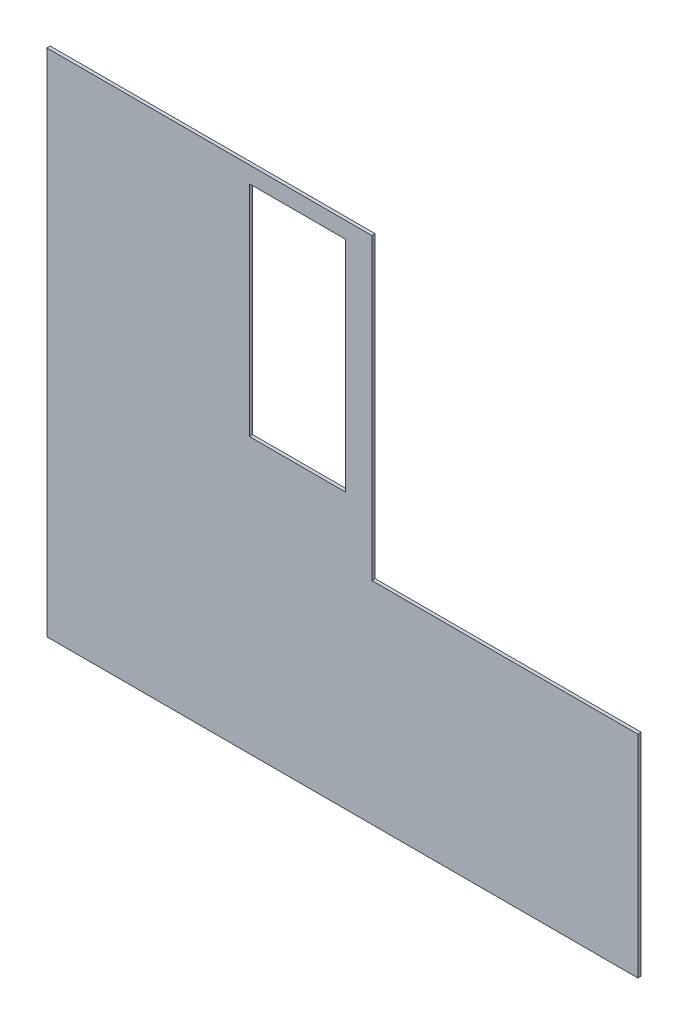
SolidWorks part; units mm, degrees
ref_plane "Plan de face" through (0, 0, 0) normal (0, 0, 1) x (1, 0, 0)
ref_plane "Plan de dessus" through (0, 0, 0) normal (0, 1, 0) x (1, 0, 0)
ref_plane "Plan de droite" through (0, 0, 0) normal (1, 0, 0) x (0, 0, -1)
sketch "Esquisse1" plane through (0, 0, 0) normal (0, 0, 1) x (1, 0, 0)
  line L0 (589.2231, -367.6438) -> (49.2231, -367.6438)
  line L1 (49.2231, 98.3562) -> (346.2231, 98.3562)
  line L2 (49.2231, 98.3562) -> (49.2231, -367.6438)
  line L4 (346.2231, 98.3562) -> (346.2231, -174.6438)
  line L5 (322.2231, -116.6438) -> (234.2231, -116.6438)
  line L6 (322.2231, -116.6438) -> (322.2231, 83.3562)
  line L7 (322.2231, 83.3562) -> (234.2231, 83.3562)
  line L8 (234.2231, -116.6438) -> (234.2231, 83.3562)
  line L11 (346.2231, -174.6438) -> (589.2231, -174.6438)
  line L12 (589.2231, -367.6438) -> (589.2231, -174.6438)
  dimension "D2" = 466
  dimension "D3" = 200
  dimension "D4" = 88
  dimension "D5" = 15
  dimension "D6" = 185
  dimension "D7" = 243
  dimension "D8" = 193
  dimension "D1" = 540
extrude "Boss.-Extru.1" add sketch "Esquisse1" along normal blind 3
equation "\"EpaisseurPlaque\"= 3"
equation "\"D1@Boss.-Extru.1\"=\"EpaisseurPlaque\""
equation "\"ProfondeurBoite\"=460"
equation "\"LongueurSyphon\"=270"
equation "\"LargeurSyphon\"=120"
equation "\"HauteurCoteDroit\"= 490"
equation "\"HauteurCoteGauche\"= 540"
equation "\"HauteurSolSyphon\"= 300"
equation "\"HauteurSyphon\"=\"HauteurCoteGauche\"-\"HauteurSolSyphon\""
equation "\"LargeurBoite\"= \"LargeurDroite\" + \"LargeurGauche\" + \"LargeurSyphon\""
equation "\"D2@Esquisse1\"=\"ProfondeurBoite\" + 2 * \"EpaisseurPlaque\""
equation "\"D1@Esquisse1\"=\"HauteurCoteGauche\""
equation "\"LargeurDroite\"=10"
equation "\"LargeurGauche\"=150"
equation "\"D7@Esquisse1\"=\"HauteurSyphon\" + \"EpaisseurPlaque\""
equation "\"D8@Esquisse1\"=\"ProfondeurBoite\" - \"LongueurSyphon\" + \"EpaisseurPlaque\""
